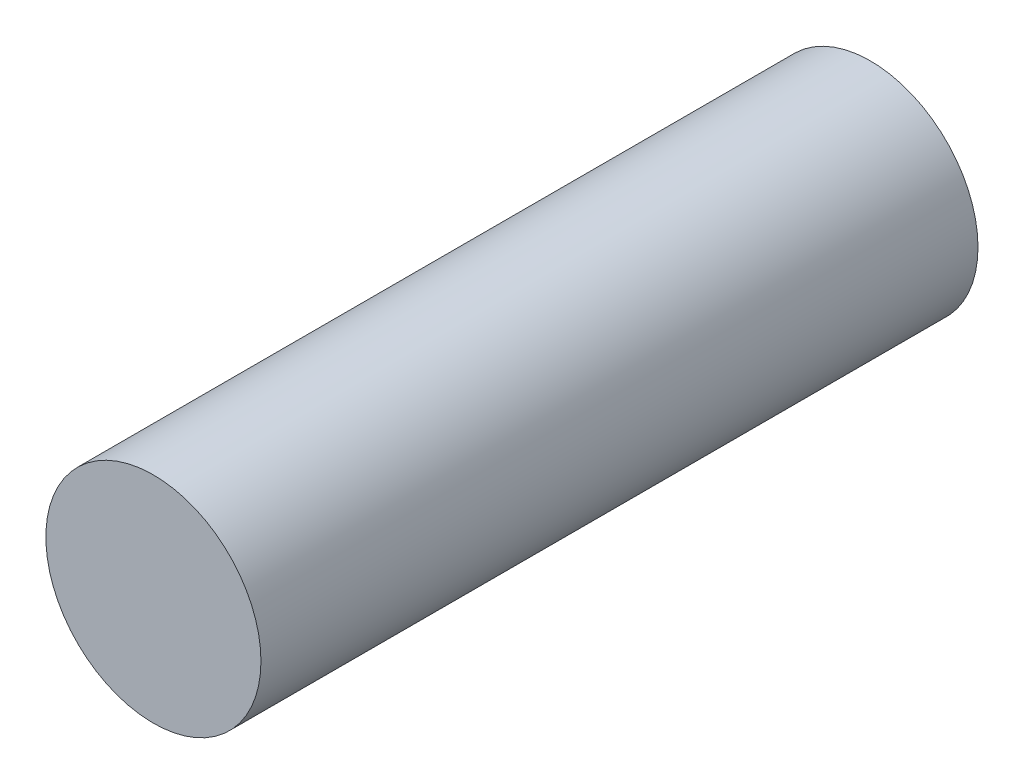
SolidWorks part; units mm, degrees
material "Erable"
ref_plane "Plan de face" through (0, 0, 0) normal (0, 0, 1) x (1, 0, 0)
ref_plane "Plan de dessus" through (0, 0, 0) normal (0, 1, 0) x (1, 0, 0)
ref_plane "Plan de droite" through (0, 0, 0) normal (1, 0, 0) x (0, 0, -1)
sketch "Esquisse1" plane through (0, 0, 0) normal (0, 0, 1) x (1, 0, 0)
  circle A0 centre (0, 0) radius 42
  dimension "D1" = 84
extrude "Boss.-Extru.1" add sketch "Esquisse1" along normal blind 280
